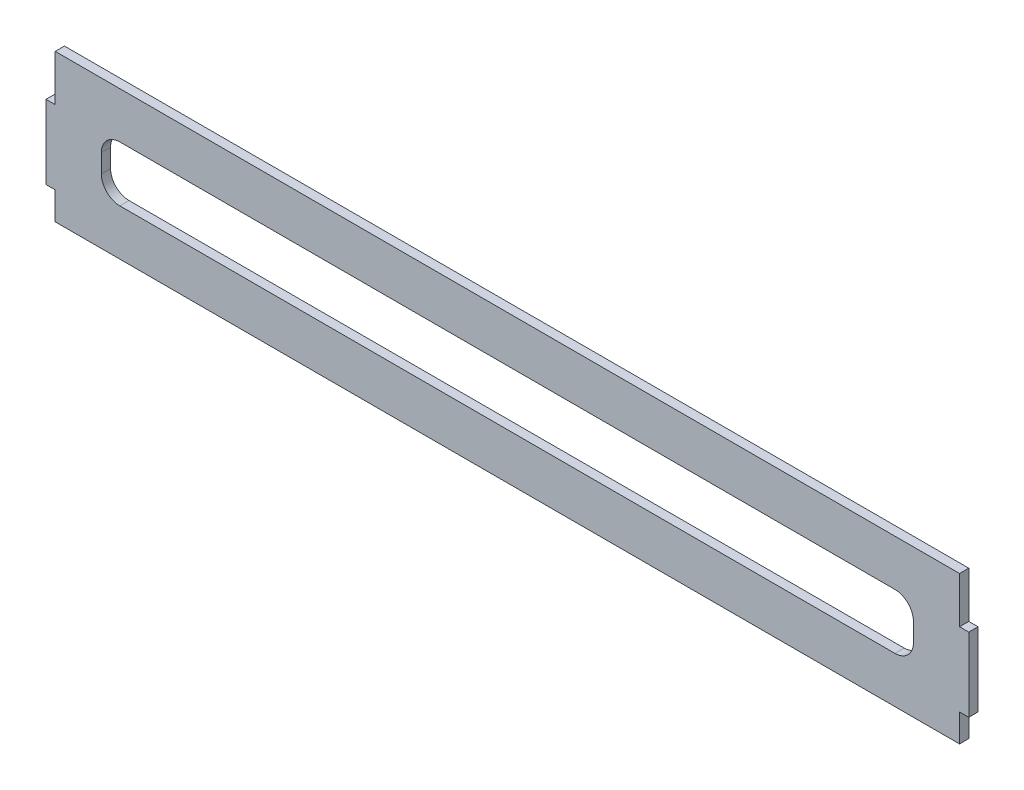
SolidWorks part; units mm, degrees
material "Contreplaqué pin"
ref_plane "Plan de face" through (0, 0, 0) normal (0, 0, 1) x (1, 0, 0)
ref_plane "Plan de dessus" through (0, 0, 0) normal (0, 1, 0) x (1, 0, 0)
ref_plane "Plan de droite" through (0, 0, 0) normal (1, 0, 0) x (0, 0, -1)
sketch "Esquisse1" plane through (0, 0, 0) normal (0, 0, 1) x (1, 0, 0)
  line L0 (0, 0) -> (0, 15)
  line L1 (0, 15) -> (-5, 15)
  line L2 (-5, 15) -> (-5, 55)
  line L3 (-5, 55) -> (0, 55)
  line L4 (0, 55) -> (0, 80)
  line L5 (0, 80) -> (490, 80)
  line L6 (490, 80) -> (490, 55)
  line L7 (490, 55) -> (495, 55)
  line L8 (495, 55) -> (495, 15)
  line L9 (495, 15) -> (490, 15)
  line L10 (490, 15) -> (490, 0)
  line L11 (490, 0) -> (0, 0)
  dimension "D1" = 40
  dimension "D2" = 5
  dimension "D3" = 80
  dimension "D4" = 15
  dimension "D5" = 490
extrude "Boss.-Extru.1" add sketch "Esquisse1" along normal blind 5
sketch "Esquisse2" plane through (0, 0, 5) normal (0, 0, 1) x (1, 0, 0)
  line L1 (35, 25) -> (455, 25)
  line L2 (25, 35) -> (25, 45)
  line L3 (35, 55) -> (455, 55)
  line L4 (465, 35) -> (465, 45)
  line L6 (0, 0) -> (490, 0) construction
  line L7 (490, 80) -> (0, 80) construction
  line L8 (0, 0) -> (0, 80) construction
  line L9 (490, 0) -> (490, 80) construction
  line L10 (0, 40) -> (25, 40) construction
  line L11 (465, 40) -> (490, 40) construction
  arc A0 (465, 35) -> (455, 25) centre (455, 35) cw
  arc A1 (465, 45) -> (455, 55) centre (455, 45) ccw
  arc A2 (35, 25) -> (25, 35) centre (35, 35) cw
  arc A3 (35, 55) -> (25, 45) centre (35, 45) ccw
  point P10 (0, 40)
  point P11 (25, 40)
  dimension "D3" = 10
  dimension "D1" = 440
  dimension "D2" = 30
extrude "Enlèv. mat.-Extru.1" cut sketch "Esquisse2" against normal up to next
